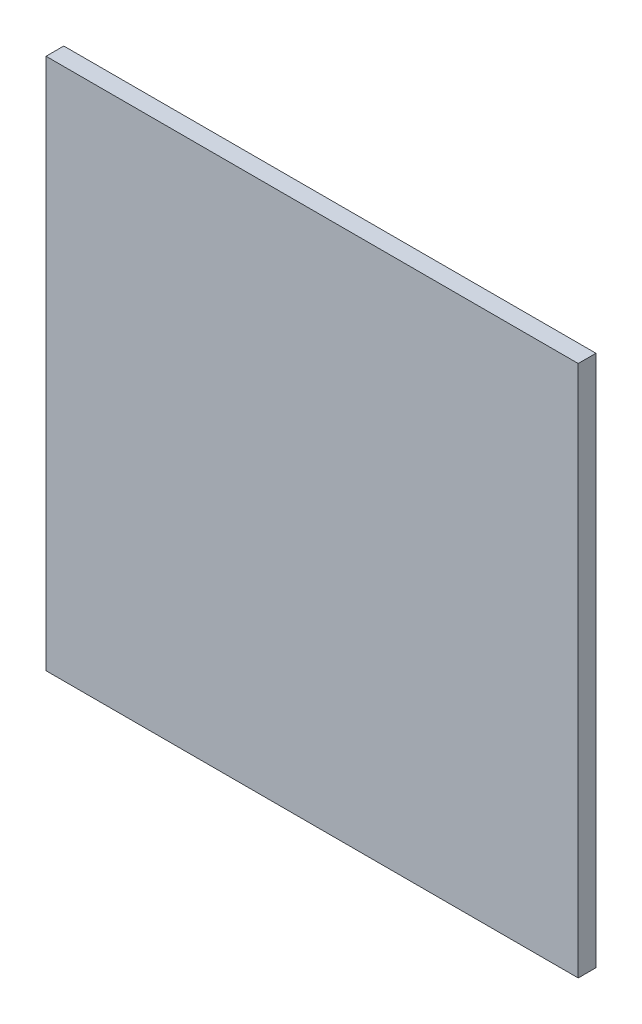
SolidWorks part; units mm, degrees
ref_plane "Plan de face" through (0, 0, 0) normal (0, 0, 1) x (1, 0, 0)
ref_plane "Plan de dessus" through (0, 0, 0) normal (0, 1, 0) x (1, 0, 0)
ref_plane "Plan de droite" through (0, 0, 0) normal (1, 0, 0) x (0, 0, -1)
sketch "Esquisse1" plane through (0, 0, 0) normal (0, 0, 1) x (1, 0, 0)
  line L1 (0, 0) -> (120, 0)
  line L2 (0, 0) -> (0, 120)
  line L3 (0, 120) -> (120, 120)
  line L4 (120, 0) -> (120, 120)
  dimension "D1" = 120
extrude "Boss.-Extru.1" add sketch "Esquisse1" along normal blind 4
